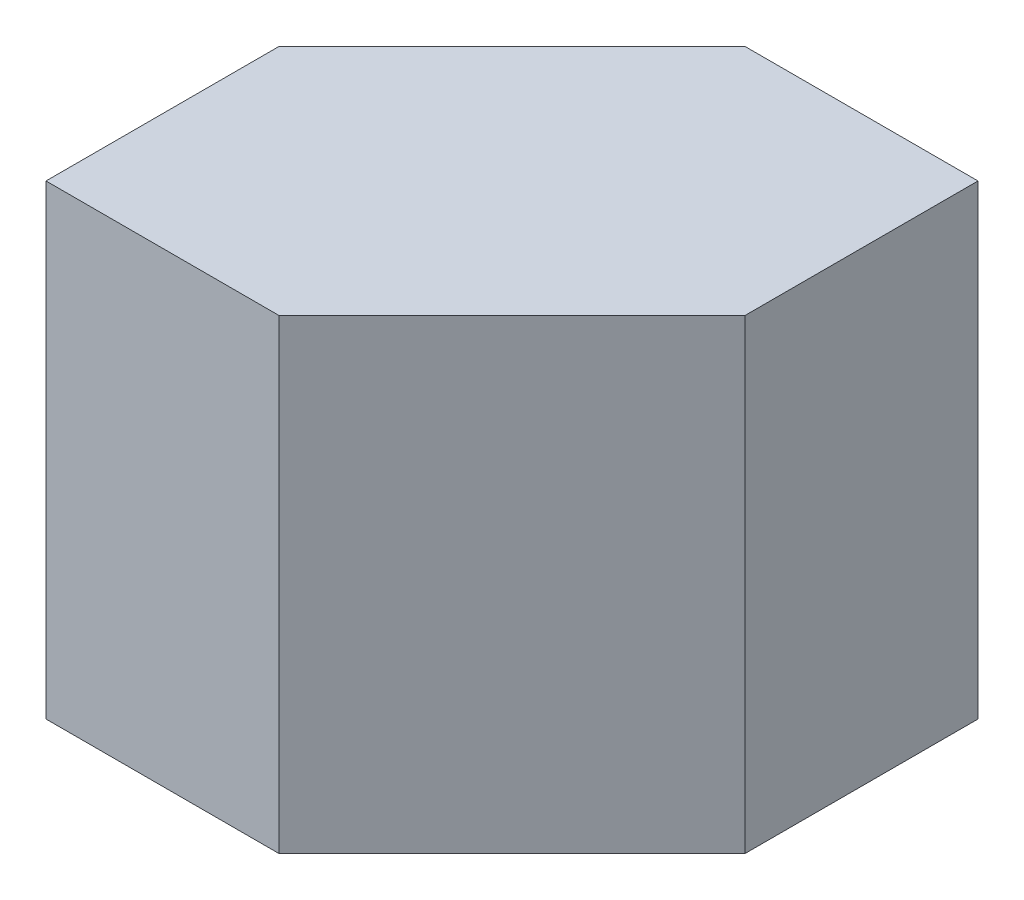
SolidWorks part; units mm, degrees
ref_plane "Front Plane" through (0, 0, 0) normal (0, 0, 1) x (1, 0, 0)
ref_plane "Top Plane" through (0, 0, 0) normal (0, 1, 0) x (1, 0, 0)
ref_plane "Right Plane" through (0, 0, 0) normal (1, 0, 0) x (0, 0, -1)
sketch "Sketch1" plane through (0, 0, 0) normal (0, 0, 1) x (1, 0, 0)
  line L1 (0, 0) -> (20, 0)
  line L2 (0, 0) -> (0, 20)
  line L3 (0, 20) -> (20, 20)
  line L4 (20, 0) -> (20, 20)
  dimension "D1" = 20
  dimension "D2" = 20
extrude "Boss-Extrude1" add sketch "Sketch1" along normal blind 20
sketch "Sketch2" plane through (0, 20, 0) normal (0, 1, 0) x (1, 0, 0)
  line L0 (20, -20) -> (20, -10)
  line L1 (20, -20) -> (20, 0) construction
  line L2 (20, -10) -> (10, -20)
  line L3 (20, -20) -> (0, -20) construction
  line L4 (10, -20) -> (20, -20)
extrude "Cut-Extrude1" cut sketch "Sketch2" against normal blind 20
sketch "Sketch3" plane through (0, 20, 0) normal (0, 1, 0) x (1, 0, 0)
  line L0 (0, 0) -> (10, 0)
  line L1 (20, 0) -> (0, 0) construction
  line L2 (10, 0) -> (0, -10)
  line L3 (0, -20) -> (0, 0) construction
  line L4 (0, -10) -> (0, 0)
extrude "Cut-Extrude2" cut sketch "Sketch3" against normal blind 20
